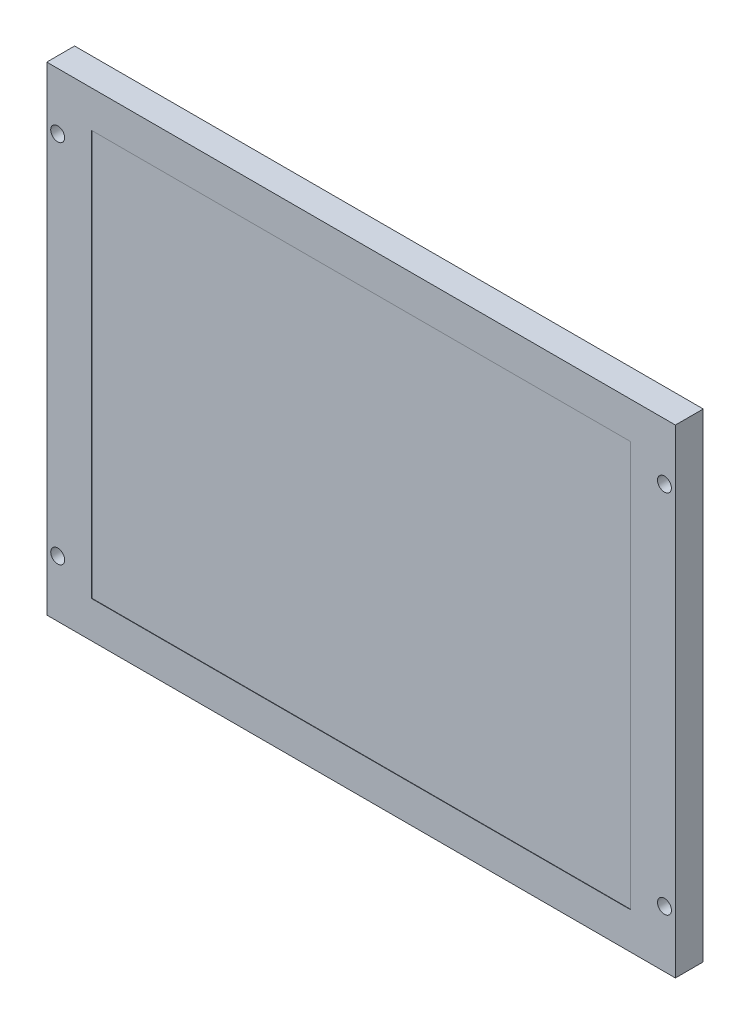
SolidWorks part; units mm, degrees
ref_plane "Front" through (0, 0, 0) normal (0, 0, 1) x (1, 0, 0)
ref_plane "Top" through (0, 0, 0) normal (0, 1, 0) x (1, 0, 0)
ref_plane "Right" through (0, 0, 0) normal (1, 0, 0) x (0, 0, -1)
sketch "Sketch1" plane through (0, 0, 0) normal (0, 0, 1) x (1, 0, 0)
  line L1 (0, 0) -> (158, 0)
  line L2 (0, 0) -> (0, -120.36)
  line L3 (0, -120.36) -> (158, -120.36)
  line L4 (158, 0) -> (158, -120.36)
  dimension "D1" = 158
  dimension "D2" = 120.36
extrude "Extrude1" add sketch "Sketch1" along normal blind 7
sketch "Sketch2" plane through (0, 0, 7) normal (0, 0, 1) x (1, 0, 0)
  line L0 (158, -120.36) -> (158, 0) construction
  line L1 (11.27, -9.23) -> (146.73, -9.23)
  line L2 (11.27, -9.23) -> (11.27, -111.13)
  line L3 (11.27, -111.13) -> (146.73, -111.13)
  line L4 (146.73, -9.23) -> (146.73, -111.13)
  line L5 (158, 0) -> (0, 0) construction
  dimension "D1" = 135.46
  dimension "D2" = 101.9
  dimension "D3" = 11.27
  dimension "D4" = 9.23
extrude "Bezel Opening" cut sketch "Sketch2" against normal blind 0.1
sketch "Sketch3" plane through (0, 0, 7) normal (0, 0, 1) x (1, 0, 0)
  line L0 (0, -120.36) -> (158, -120.36) construction
  line L1 (0, 0) -> (0, -120.36) construction
  circle A0 centre (155.25, -14.23) radius 1.75
  circle A1 centre (155.25, -106.13) radius 1.75
  circle A2 centre (2.75, -14.23) radius 1.75
  circle A3 centre (2.75, -106.13) radius 1.75
  dimension "D1" = 3.5
  dimension "D3" = 3.5
  dimension "D2" = 3.5
  dimension "D4" = 3.5
  dimension "D5" = 91.9
  dimension "D6" = 14.23
  dimension "D7" = 2.75
  dimension "D8" = 152.5
extrude "Mount hole cut" cut sketch "Sketch3" against normal blind 10
sketch "Center lines" plane through (0, 0, 7) normal (0, 0, 1) x (1, 0, 0)
  line L0 (79, 0) -> (79, -120.36) construction
  line L1 (158, 0) -> (0, 0) construction
  line L2 (0, -120.36) -> (158, -120.36) construction
  line L6 (158, -60.18) -> (0, -60.18) construction
  line L7 (158, -120.36) -> (158, 0) construction
  line L8 (0, 0) -> (0, -120.36) construction
sketch "Sketch4" plane through (0, 0, 0) normal (0, 0, -1) x (-1, 0, 0)
  line L0 (-122.9287, -77.66) -> (-142.5713, -77.66) construction
  line L1 (-142.5713, -75.8185) -> (-122.9287, -75.8185)
  line L2 (-142.5713, -75.8185) -> (-142.5713, -79.5015)
  line L3 (-142.5713, -79.5015) -> (-122.9287, -79.5015)
  line L4 (-122.9287, -75.8185) -> (-122.9287, -79.5015)
  line L5 (-132.75, -75.8185) -> (-132.75, -79.5015) construction
  line L6 (-158, -120.36) -> (-158, 0) construction
  line L7 (0, -120.36) -> (-158, -120.36) construction
  point P8 (-132.75, -77.66)
  dimension "D1" = 25.25
  dimension "D2" = 42.7
extrude "Hirose DF9 connector" add sketch "Sketch4" along normal blind 3.75
